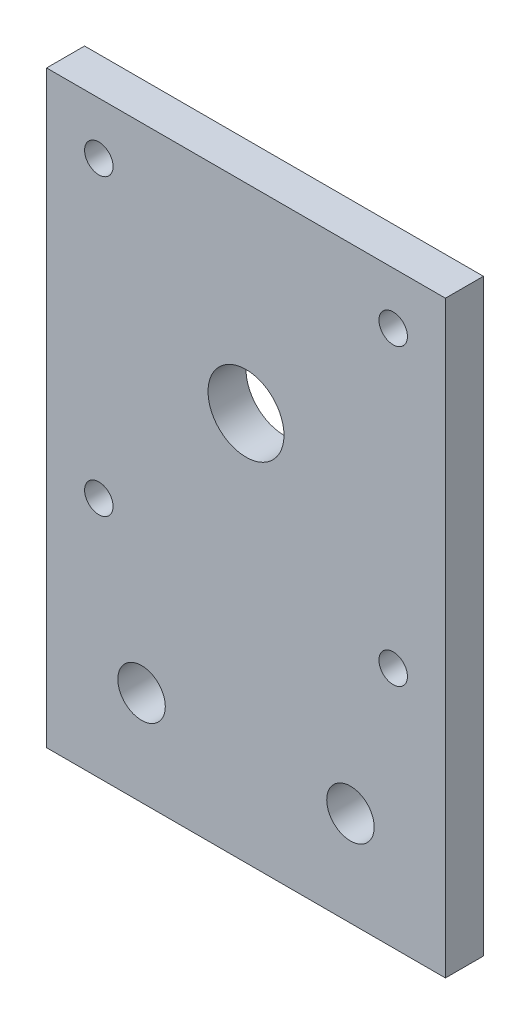
SolidWorks part; units mm, degrees
ref_plane "Front Plane" through (0, 0, 0) normal (0, 0, 1) x (1, 0, 0)
ref_plane "Top Plane" through (0, 0, 0) normal (0, 1, 0) x (1, 0, 0)
ref_plane "Right Plane" through (0, 0, 0) normal (1, 0, 0) x (0, 0, -1)
sketch "Sketch1" plane through (0, 0, 0) normal (0, 0, 1) x (1, 0, 0)
  line L1 (21, -21) -> (-21, -21)
  line L2 (21, -21) -> (21, 21)
  line L3 (21, 21) -> (-21, 21)
  line L4 (-21, -21) -> (-21, 21)
  line L5 (21, -21) -> (-21, 21) construction
  line L6 (21, 21) -> (-21, -21) construction
  line L11 (15.5, -15.5) -> (-15.5, 15.5) construction
  line L12 (15.5, 15.5) -> (-15.5, -15.5) construction
  circle A0 centre (0, 0) radius 4
  circle A1 centre (-15.5, 15.5) radius 1.5
  circle A2 centre (15.5, 15.5) radius 1.5
  circle A3 centre (15.5, -15.5) radius 1.5
  circle A4 centre (-15.5, -15.5) radius 1.5
  point P0 (0, 0)
  point P22 (0, 0)
  dimension "D3" = 31
  dimension "D4" = 8
  dimension "D5" = 4
  dimension "D1" = 42
  dimension "D2" = 42
extrude "Boss-Extrude1" add sketch "Sketch1" along normal blind 4
sketch "Sketch3" plane through (0, -21, 0) normal (0, -1, 0) x (1, 0, 0)
  line L1 (-21, 0) -> (21, 0) construction
  line L2 (-21, 0) -> (21, 0)
  line L3 (-21, 4) -> (-21, 0) construction
  line L4 (-21, 4) -> (-21, 0)
  line L5 (-21, 4) -> (21, 4) construction
  line L6 (-21, 4) -> (21, 4)
  line L7 (21, 4) -> (21, 0) construction
  line L8 (21, 4) -> (21, 0)
extrude "Boss-Extrude2" add sketch "Sketch3" along normal blind 20
sketch "Sketch4" plane through (0, 0, 0) normal (0, 0, -1) x (-1, 0, 0)
  line L1 (-21, -41) -> (-21, 21) construction
  line L2 (21, -41) -> (-21, -41) construction
  circle A0 centre (-11, -31) radius 2.5
  circle A1 centre (11, -31) radius 2.5
  dimension "D1" = 5
  dimension "D2" = 5
  dimension "D3" = 10
  dimension "D4" = 22
  dimension "D5" = 10
extrude "Cut-Extrude2" cut sketch "Sketch4" against normal blind 20
